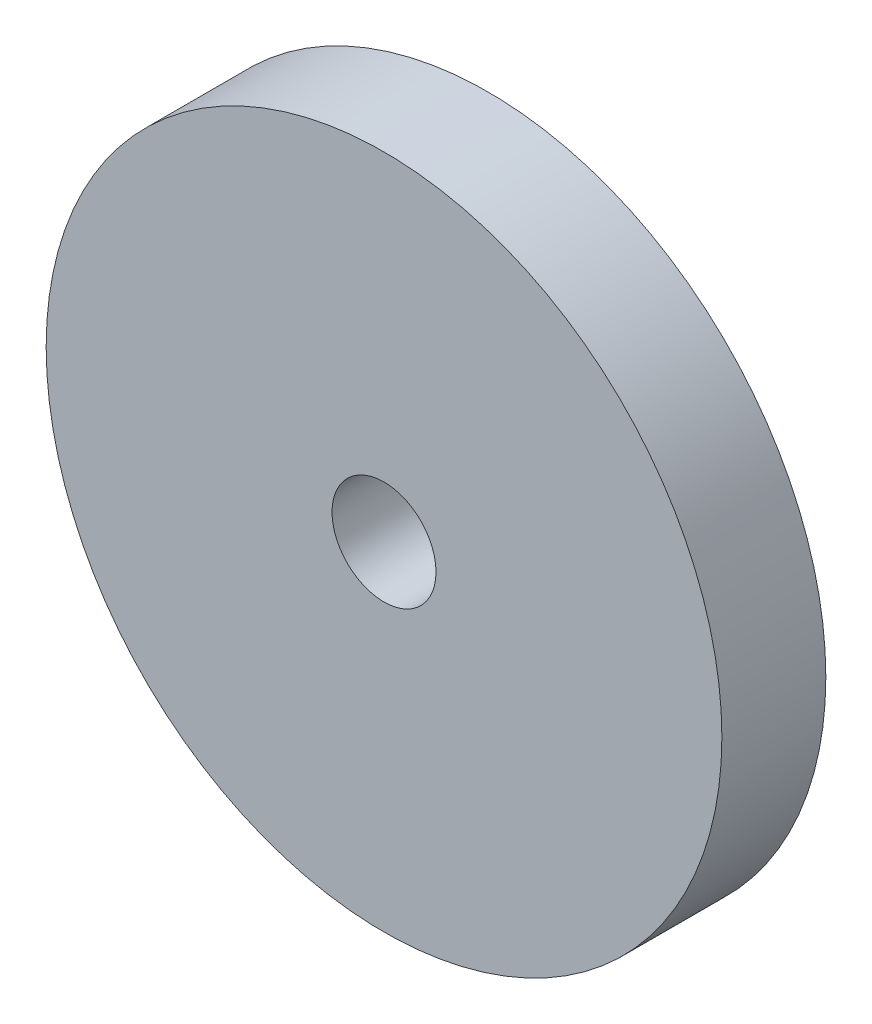
SolidWorks part; units mm, degrees
ref_plane "Front Plane" through (0, 0, 0) normal (0, 0, 1) x (1, 0, 0)
ref_plane "Top Plane" through (0, 0, 0) normal (0, 1, 0) x (1, 0, 0)
ref_plane "Right Plane" through (0, 0, 0) normal (1, 0, 0) x (0, 0, -1)
sketch "Sketch1" plane through (0, 0, 0) normal (0, 0, 1) x (1, 0, 0)
  circle A0 centre (0, 0) radius 6.35
  circle A1 centre (0, 0) radius 41.275
  dimension "D1" = 12.7
  dimension "D2" = 82.55
extrude "Boss-Extrude1" add sketch "Sketch1" along normal mid plane 12.7
